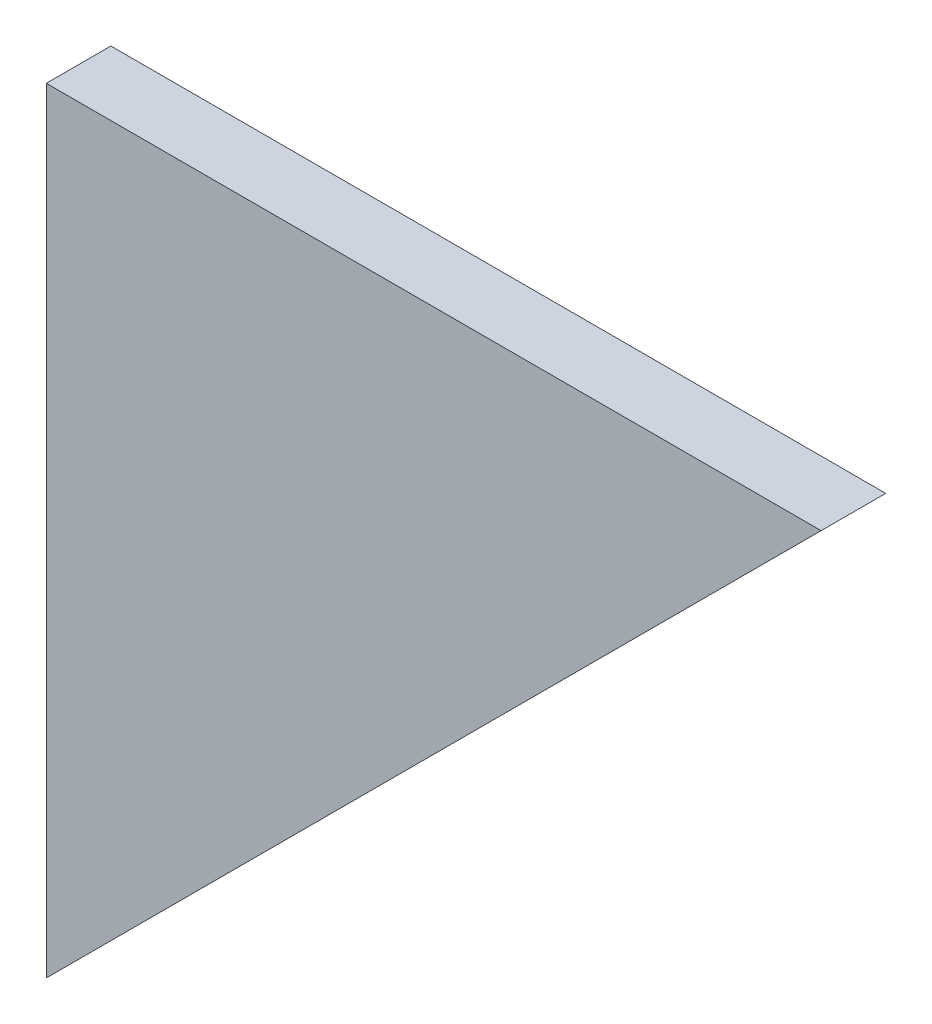
SolidWorks part; units mm, degrees
ref_plane "Front Plane" through (0, 0, 0) normal (0, 0, 1) x (1, 0, 0)
ref_plane "Top Plane" through (0, 0, 0) normal (0, 1, 0) x (1, 0, 0)
ref_plane "Right Plane" through (0, 0, 0) normal (1, 0, 0) x (0, 0, -1)
sketch "Sketch1" plane through (0, 0, 0) normal (0, 0, 1) x (1, 0, 0)
  line L0 (0, 0) -> (76.2, 0)
  line L1 (76.2, 0) -> (0, -76.2)
  line L2 (0, -76.2) -> (0, 0)
  dimension "D1" = 76.2
extrude "Boss-Extrude1" add sketch "Sketch1" along normal mid plane 6.35
